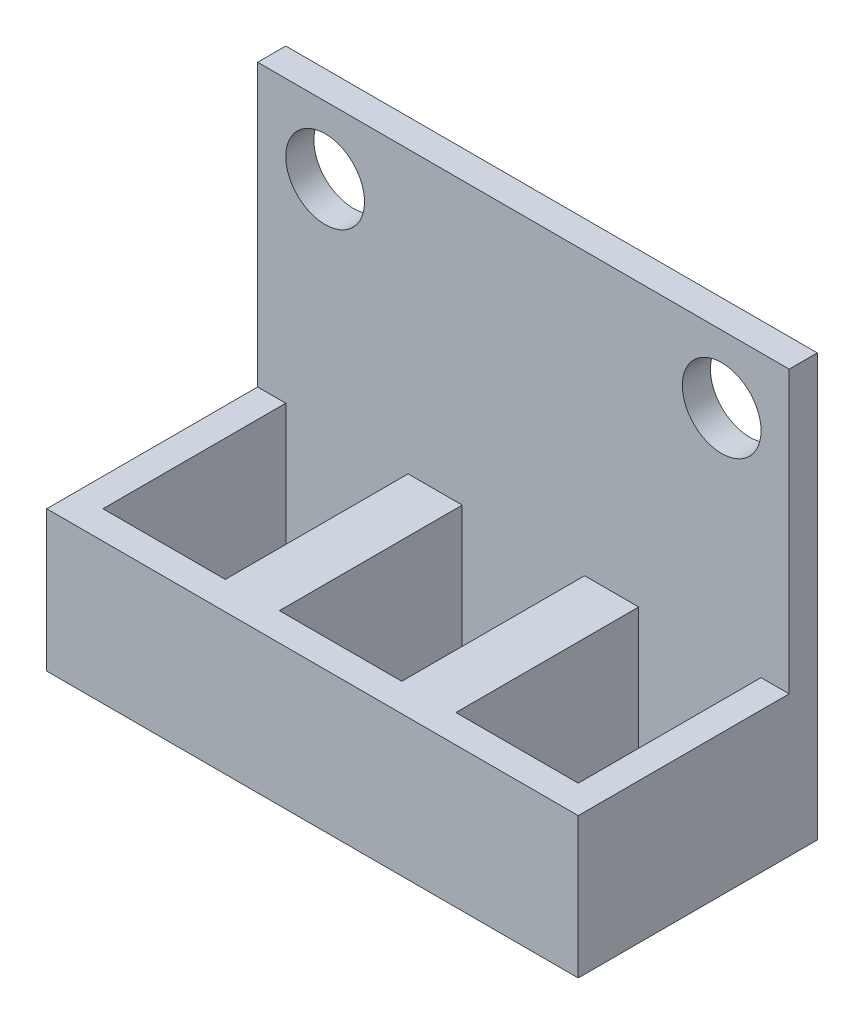
SolidWorks part; units mm, degrees
ref_plane "Front Plane" through (0, 0, 0) normal (0, 0, 1) x (1, 0, 0)
ref_plane "Top Plane" through (0, 0, 0) normal (0, 1, 0) x (1, 0, 0)
ref_plane "Right Plane" through (0, 0, 0) normal (1, 0, 0) x (0, 0, -1)
sketch "Sketch1" plane through (0, 0, 0) normal (0, 1, 0) x (1, 0, 0)
  line L1 (-9.45, -4.25) -> (9.45, -4.25)
  line L2 (-9.45, -4.25) -> (-9.45, 4.25)
  line L3 (-9.45, 4.25) -> (9.45, 4.25)
  line L4 (9.45, -4.25) -> (9.45, 4.25)
  line L5 (-9.45, -4.25) -> (9.45, 4.25) construction
  line L6 (-9.45, 4.25) -> (9.45, -4.25) construction
  line L7 (-8.45, 3.25) -> (-4.1, 3.25)
  line L8 (-8.45, 3.25) -> (-8.45, -3.25)
  line L9 (-8.45, -3.25) -> (-4.1, -3.25)
  line L10 (-4.1, 3.25) -> (-4.1, -3.25)
  line L11 (-8.45, 3.25) -> (-4.1, -3.25) construction
  line L12 (-8.45, -3.25) -> (-4.1, 3.25) construction
  line L13 (-2.175, 3.25) -> (2.175, 3.25)
  line L14 (-2.175, 3.25) -> (-2.175, -3.25)
  line L15 (-2.175, -3.25) -> (2.175, -3.25)
  line L16 (2.175, 3.25) -> (2.175, -3.25)
  line L17 (-2.175, 3.25) -> (2.175, -3.25) construction
  line L18 (-2.175, -3.25) -> (2.175, 3.25) construction
  line L19 (4.1, 3.25) -> (8.45, 3.25)
  line L20 (4.1, 3.25) -> (4.1, -3.25)
  line L21 (4.1, -3.25) -> (8.45, -3.25)
  line L22 (8.45, 3.25) -> (8.45, -3.25)
  line L23 (4.1, 3.25) -> (8.45, -3.25) construction
  line L24 (4.1, -3.25) -> (8.45, 3.25) construction
  point P0 (0, 0)
  point P6 (-6.275, 0)
  point P11 (0, 0)
  point P16 (6.275, 0)
  dimension "D1" = 18.9
  dimension "D2" = 8.5
  dimension "D3" = 6.5
  dimension "D4" = 4.35
  dimension "D5" = 4.35
  dimension "D6" = 4.35
  dimension "D7" = 16.9
  dimension "D8" = 8.45
extrude "Boss-Extrude1" add sketch "Sketch1" along normal blind 5
sketch "Sketch2" plane through (0, 5, 0) normal (0, 1, 0) x (1, 0, 0)
  line L0 (9.45, -4.25) -> (9.45, 4.25) construction
  line L1 (-9.45, 4.25) -> (9.45, 4.25)
  line L2 (-9.45, 4.25) -> (-9.45, 3.25)
  line L3 (-9.45, 3.25) -> (9.45, 3.25)
  line L4 (9.45, 4.25) -> (9.45, 3.25)
  dimension "D1" = 1
extrude "Boss-Extrude2" add sketch "Sketch2" along normal blind 10
sketch "Sketch3" plane through (0, 0, -3.25) normal (0, 0, 1) x (1, 0, 0)
  line L0 (-9.45, 15) -> (9.45, 15) construction
  line L1 (9.45, 15) -> (9.45, 5) construction
  line L3 (-9.45, 15) -> (-9.45, 5) construction
  circle A0 centre (7.05, 12.6) radius 1.4
  circle A1 centre (-7.05, 12.6) radius 1.4
  dimension "D1" = 2.8
  dimension "D2" = 2.8
  dimension "D3" = 2.4
  dimension "D4" = 2.4
  dimension "D5" = 2.4
  dimension "D6" = 2.4
extrude "Cut-Extrude1" cut sketch "Sketch3" against normal through all
